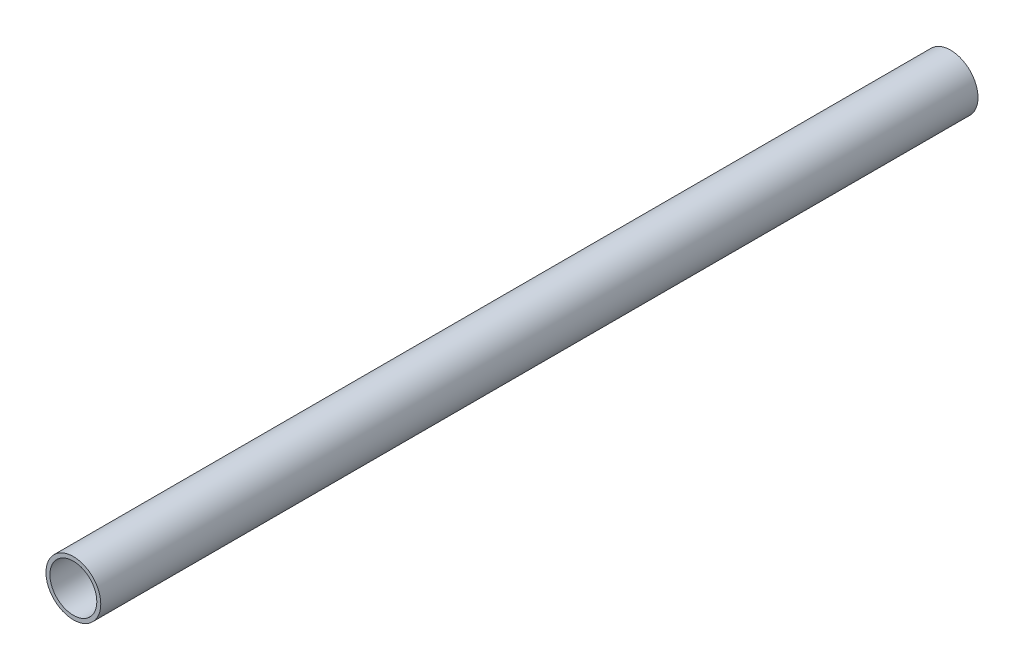
SolidWorks part; units mm, degrees
ref_plane "Front Plane" through (0, 0, 0) normal (0, 0, 1) x (1, 0, 0)
ref_plane "Top Plane" through (0, 0, 0) normal (0, 1, 0) x (1, 0, 0)
ref_plane "Right Plane" through (0, 0, 0) normal (1, 0, 0) x (0, 0, -1)
sketch "Sketch1" plane through (0, 0, 0) normal (0, 0, 1) x (1, 0, 0)
  circle A0 centre (0, 0) radius 1.5875
  dimension "D1" = 3.175
extrude "Extrude-Thin1" add sketch "Sketch1" along normal blind 50.8 thin thin type one direction reverse wall 0.2286
